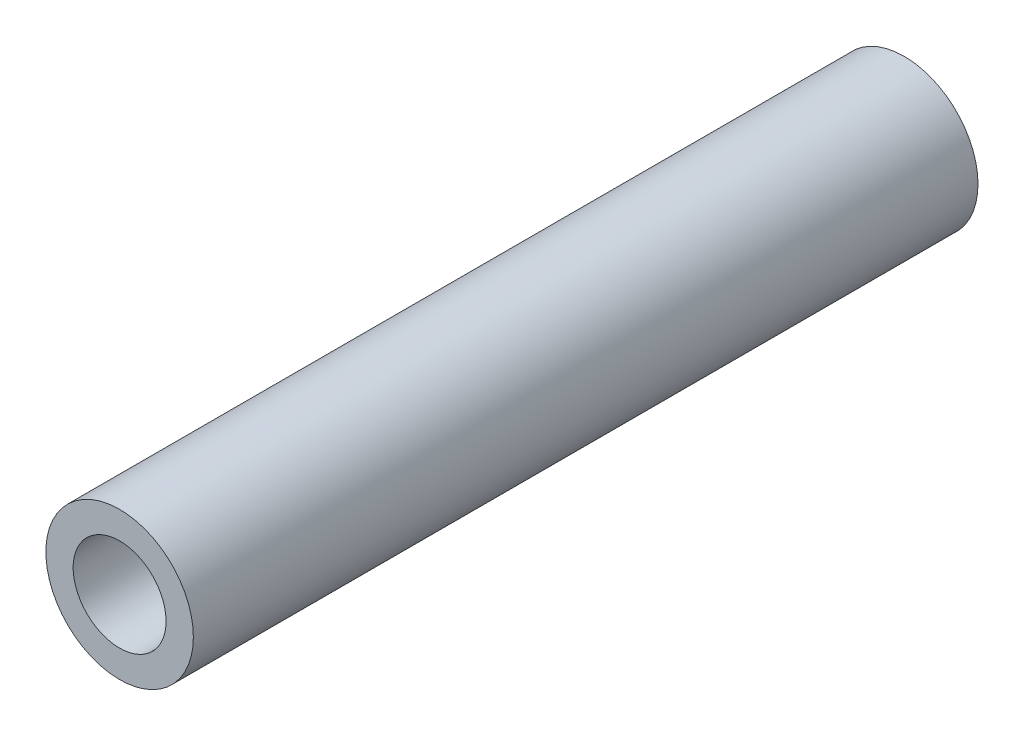
SolidWorks part; units mm, degrees
material "PET"
ref_plane "Front Plane" through (0, 0, 0) normal (0, 0, 1) x (1, 0, 0)
ref_plane "Top Plane" through (0, 0, 0) normal (0, 1, 0) x (1, 0, 0)
ref_plane "Right Plane" through (0, 0, 0) normal (1, 0, 0) x (0, 0, -1)
sketch "Sketch1" plane through (0, 0, 0) normal (0, 0, 1) x (1, 0, 0)
  circle A0 centre (0, 0) radius 3.175
  circle A1 centre (0, 0) radius 2.286
  dimension "D1" = 6.35
  dimension "D2" = 4.572
extrude "Boss-Extrude1" add sketch "Sketch1" against normal offset from surface (29.7165 mm away) 3.175
sketch "Sketch2" plane through (0, 0, -29.7165) normal (0, 0, -1) x (-1, 0, 0)
  circle A0 centre (0, 0) radius 3.175 construction
  circle A1 centre (0, 0) radius 2.286 construction
  circle A2 centre (0, 0) radius 3.175
  circle A3 centre (0, 0) radius 2.286
extrude "Boss-Extrude2" add sketch "Sketch2" along normal blind 4.064
sketch "Sketch3" plane through (0, 0, 0) normal (0, 0, 1) x (1, 0, 0)
  circle A0 centre (0, 0) radius 2
  dimension "D1" = 4
extrude "Extrude-Thin1" add sketch "Sketch3" against normal blind 12.7 draft 1 thin
